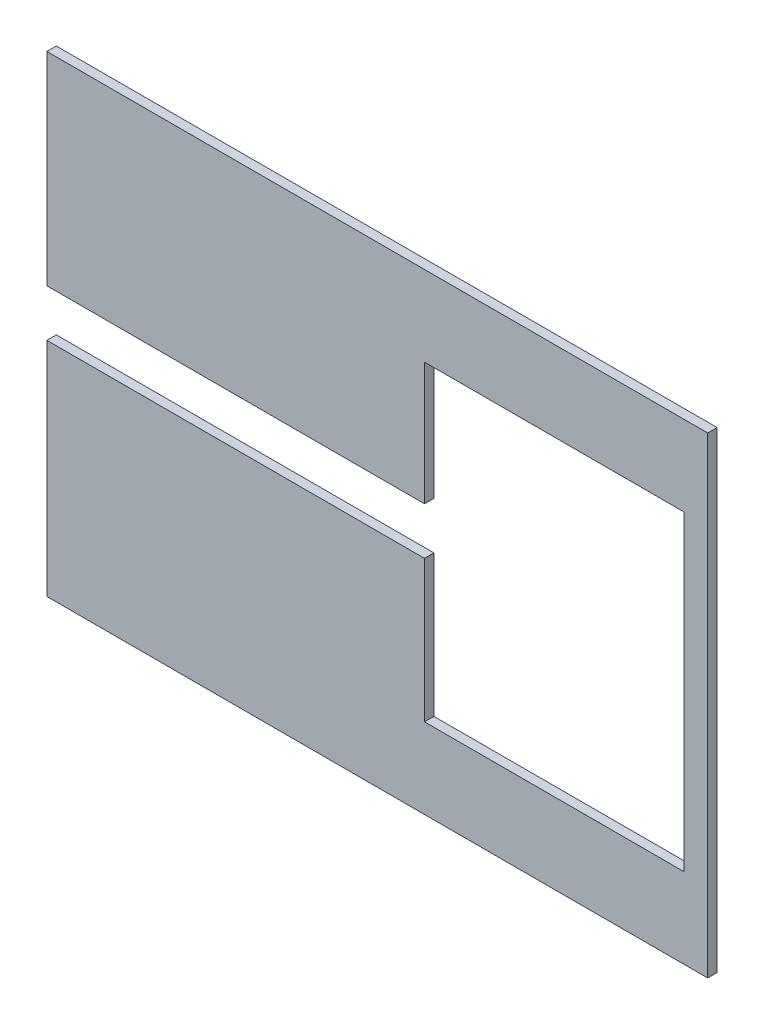
SolidWorks part; units mm, degrees
ref_plane "Plan de face" through (0, 0, 0) normal (0, 0, 1) x (1, 0, 0)
ref_plane "Plan de dessus" through (0, 0, 0) normal (0, 1, 0) x (1, 0, 0)
ref_plane "Plan de droite" through (0, 0, 0) normal (1, 0, 0) x (0, 0, -1)
sketch "Esquisse1" plane through (0, 0, 0) normal (0, 0, 1) x (1, 0, 0)
  line L1 (0, 0) -> (140, 0)
  line L2 (0, 0) -> (0, 100)
  line L3 (0, 100) -> (140, 100)
  line L4 (140, 0) -> (140, 100)
  dimension "D1" = 140
  dimension "D2" = 100
extrude "Boss.-Extru.1" add sketch "Esquisse1" along normal blind 2
sketch "Esquisse2" plane through (0, 0, 2) normal (0, 0, 1) x (1, 0, 0)
  line L0 (140, 0) -> (140, 100) construction
  line L1 (135, 83) -> (80, 83)
  line L2 (135, 83) -> (135, 17)
  line L3 (135, 17) -> (80, 17)
  line L4 (80, 83) -> (80, 17)
  line L5 (0, 0) -> (140, 0) construction
  dimension "D1" = 5
  dimension "D2" = 55
  dimension "D3" = 66
  dimension "D4" = 17
extrude "Enlèv. mat.-Extru.1" cut sketch "Esquisse2" against normal blind 2
sketch "Esquisse3" plane through (0, 0, 2) normal (0, 0, 1) x (1, 0, 0)
  line L1 (80, 83) -> (135, 83)
  line L2 (80, 83) -> (80, 17)
  line L3 (80, 17) -> (135, 17)
  line L4 (135, 83) -> (135, 17)
  line L5 (78, 85) -> (137, 85)
  line L6 (78, 85) -> (78, 15)
  line L7 (78, 15) -> (137, 15)
  line L8 (137, 85) -> (137, 15)
  line L9 (80, 57) -> (0, 57)
  line L10 (80, 57) -> (80, 47)
  line L11 (80, 47) -> (0, 47)
  line L12 (0, 57) -> (0, 47)
  line M15 (0, 100) -> (0, 0)
  dimension "D1" = 2
  dimension "D2" = 2
  dimension "D3" = 2
  dimension "D4" = 2
  dimension "D5" = 10
  dimension "D6" = 28
  dimension "D7" = 80
extrude "Enlèv. mat.-Extru.2" cut sketch "Esquisse3" against normal blind 3 contours L11 L6 L9 M15 | L11 L2 L9 L6
